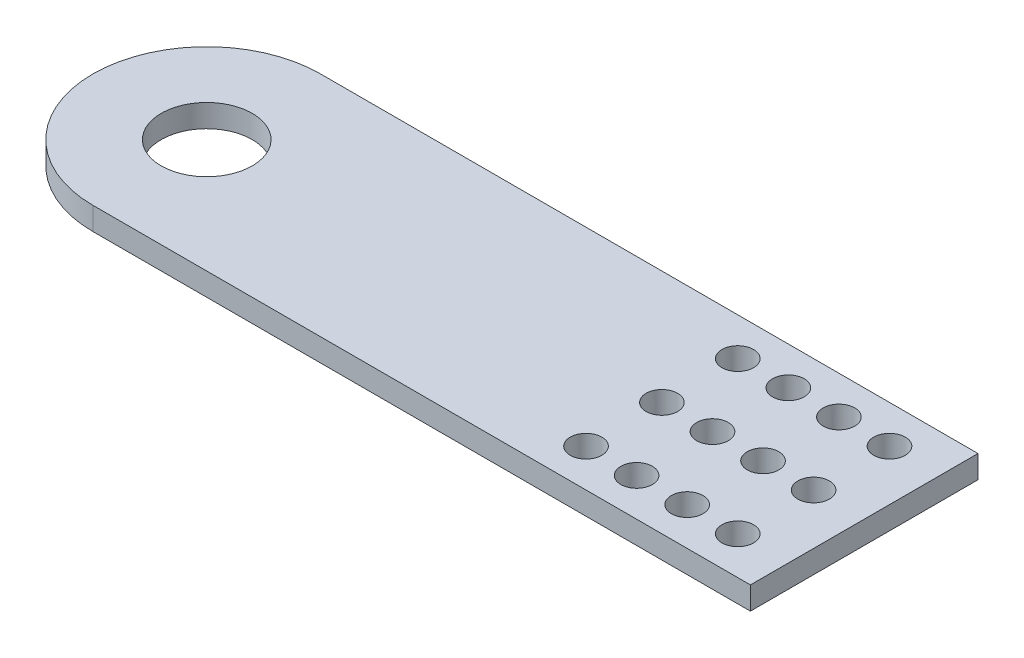
SolidWorks part; units mm, degrees
ref_plane "Front Plane" through (0, 0, 0) normal (0, 0, 1) x (1, 0, 0)
ref_plane "Top Plane" through (0, 0, 0) normal (0, 1, 0) x (1, 0, 0)
ref_plane "Right Plane" through (0, 0, 0) normal (1, 0, 0) x (0, 0, -1)
sketch "Sketch1" plane through (0, 0, 0) normal (0, 1, 0) x (1, 0, 0)
  line L0 (0, 0) -> (65, 0) construction
  line L1 (130, -22.5) -> (0, -22.5)
  line L2 (130, -22.5) -> (130, 22.5)
  line L3 (0, -22.5) -> (0, 22.5) construction
  line L4 (130, 22.5) -> (0, 22.5)
  line L5 (0, 0) -> (130, 0) construction
  line L6 (65, -22.5) -> (65, 22.5) construction
  line L8 (0, 22.5) -> (-30, 22.5)
  line L9 (0, 22.5) -> (0, -22.5) construction
  line L10 (0, -22.5) -> (-30, -22.5)
  line L11 (-30, 22.5) -> (-30, -22.5)
  line L12 (-15, -22.5) -> (-15, 22.5) construction
  line L13 (0, 0) -> (-30, 0) construction
  circle A0 centre (0, 0) radius 9
  point P93 (-15, 0)
  dimension "D1" = 18
  dimension "D2" = 130
  dimension "D3" = 45
  dimension "D4" = 30
extrude "Boss-Extrude1" add sketch "Sketch1" along normal mid plane 4.5
sketch "Sketch2" plane through (0, 2.25, 0) normal (0, 1, 0) x (1, 0, 0)
  line L0 (130, 0) -> (0, 0) construction
  line L1 (130, -22.5) -> (130, 22.5) construction
  circle A0 centre (120, 0) radius 3.125
  dimension "D1" = 6.25
  dimension "D2" = 10
extrude "Cut-Extrude1" cut sketch "Sketch2" against normal through all both and the other way through all
pattern_linear "LPattern1" count 4 spacing 10 along (-1, 0, 0) of "Cut-Extrude1"
pattern_linear "LPattern2" count 2 spacing 15 along (0, 0, 1) count 2 spacing 15 along (0, 0, -1) of "LPattern1", "Cut-Extrude1"
sketch "Sketch3" plane through (0, 2.25, 0) normal (0, 1, 0) x (1, 0, 0)
  line L2 (0, -47.3206) -> (0, 47.3206) construction
  circle A0 centre (0, 0) radius 22.5
  arc A1 (0, 47.3206) -> (0, -47.3206) centre (0, 0) ccw
  point P5 (0.8885, -32.9244)
  point P8 (0, 0)
  line M12 (-30, 22.5) -> (-30, -22.5)
  line M13 (-30, -22.5) -> (130, -22.5)
  line M15 (130, 22.5) -> (-30, 22.5)
extrude "Cut-Extrude2" cut sketch "Sketch3" against normal through all both and the other way through all contours A0 M15 M12 M13
